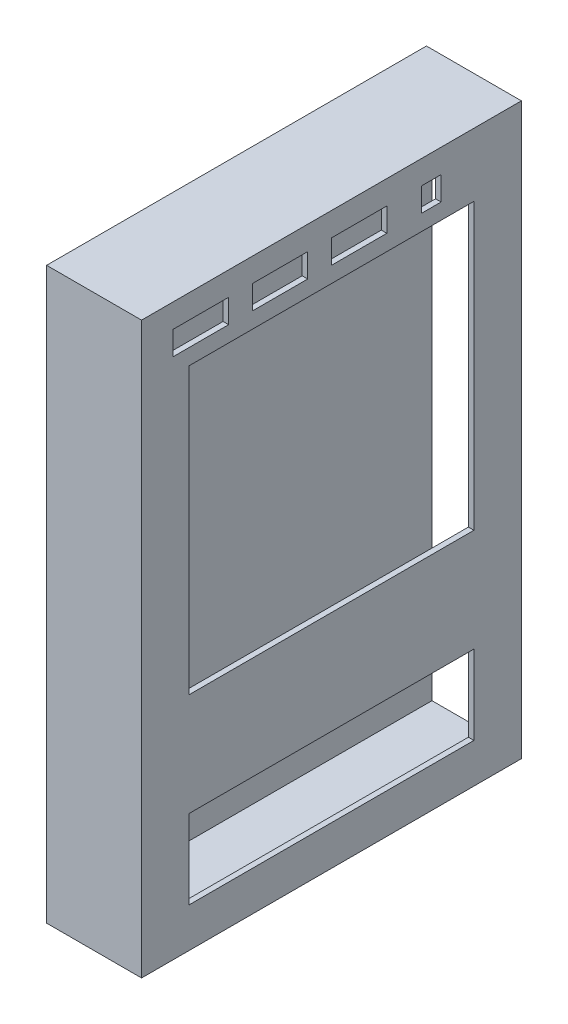
SolidWorks part; units mm, degrees
ref_plane "Front Plane" through (0, 0, 0) normal (0, 0, 1) x (1, 0, 0)
ref_plane "Top Plane" through (0, 0, 0) normal (0, 1, 0) x (1, 0, 0)
ref_plane "Right Plane" through (0, 0, 0) normal (1, 0, 0) x (0, 0, -1)
sketch "Sketch1" plane through (0, 0, 0) normal (1, 0, 0) x (0, 0, -1)
  line L0 (-304.8, 0) -> (304.8, 0) construction
  line L3 (-304.8, 0) -> (304.8, 0)
  line L4 (-304.8, 0) -> (-304.8, 914.4)
  line L5 (-304.8, 914.4) -> (304.8, 914.4)
  line L6 (304.8, 0) -> (304.8, 914.4)
  point P4 (0, 0)
  dimension "D1" = 609.6
  dimension "D2" = 914.4
extrude "OuterBodie" add sketch "Sketch1" against normal blind 152.4
shell "Shell1" thickness 8.89
sketch "Sketch2" plane through (0, 0, 0) normal (1, 0, 0) x (0, 0, -1)
  line L0 (0, 0) -> (0, 342.9) construction
  line L4 (-228.6, 355.6) -> (228.6, 355.6)
  line L6 (-228.6, 812.8) -> (228.6, 812.8)
  line L9 (304.8, 914.4) -> (-304.8, 914.4) construction
  line L10 (-228.6, 812.8) -> (-228.6, 355.6)
  line L11 (228.6, 812.8) -> (228.6, 355.6)
  line L12 (-304.8, 914.4) -> (-304.8, 0) construction
  line L13 (-304.8, 0) -> (304.8, 0) construction
  dimension "D1" = 457.2
  dimension "D2" = 101.6
  dimension "D3" = 457.2
  dimension "D4" = 76.2
  dimension "D5" = 355.6
sketch "Sketch3" plane through (0, 0, 0) normal (1, 0, 0) x (0, 0, -1)
  line L0 (0, 0) -> (0, 63.5) construction
  line L1 (-228.6, 190.5) -> (-228.6, 63.5) construction
  line L3 (228.6, 190.5) -> (228.6, 63.5) construction
  line L5 (-228.6, 63.5) -> (228.6, 63.5)
  line L6 (-228.6, 63.5) -> (-228.6, 190.5)
  line L7 (-228.6, 190.5) -> (228.6, 190.5)
  line L8 (228.6, 63.5) -> (228.6, 190.5)
  dimension "D1" = 63.5
  dimension "D2" = 127
  dimension "D3" = 457.2
extrude "Wire duct" cut sketch "Sketch3" against normal up to surface (8.89 mm away) up to face at (-8.89, 457.2, -4.445)
extrude "Display cutout" cut sketch "Sketch2" against normal up to surface (8.89 mm away) up to face at (-8.89, 127, 0)
sketch "Sketch5" plane through (0, 0, 0) normal (1, 0, 0) x (0, 0, -1)
  line L0 (-304.8, 838.2) -> (304.8, 838.2) construction
  line L1 (-304.8, 914.4) -> (-304.8, 0) construction
  line L2 (304.8, 0) -> (304.8, 914.4) construction
  line L3 (304.8, 914.4) -> (-304.8, 914.4) construction
  line L5 (-254, 838.2) -> (-165.1, 838.2)
  line L6 (-254, 838.2) -> (-254, 876.3)
  line L7 (-254, 876.3) -> (-165.1, 876.3)
  line L8 (-165.1, 838.2) -> (-165.1, 876.3)
  line L9 (-127, 838.2) -> (-127, 876.3)
  line L10 (-127, 838.2) -> (-38.1, 838.2)
  line L11 (-38.1, 838.2) -> (-38.1, 876.3)
  line L12 (-127, 876.3) -> (-38.1, 876.3)
  line L13 (0, 838.2) -> (0, 876.3)
  line L14 (0, 838.2) -> (88.9, 838.2)
  line L15 (88.9, 838.2) -> (88.9, 876.3)
  line L16 (0, 876.3) -> (88.9, 876.3)
  line L18 (144.1513, 838.2) -> (175.9013, 838.2)
  line L19 (144.1513, 838.2) -> (144.1513, 876.3)
  line L20 (144.1513, 876.3) -> (175.9013, 876.3)
  line L21 (175.9013, 838.2) -> (175.9013, 876.3)
  dimension "D1" = 76.2
  dimension "D2" = 50.8
  dimension "D3" = 88.9
  dimension "D4" = 38.1
  dimension "D6" = 38.1
  dimension "D7" = 31.75
  dimension "D5" = 3
extrude "Game Display" cut sketch "Sketch5" against normal up to surface (8.89 mm away) up to face at (-8.89, 584.2, 0)
